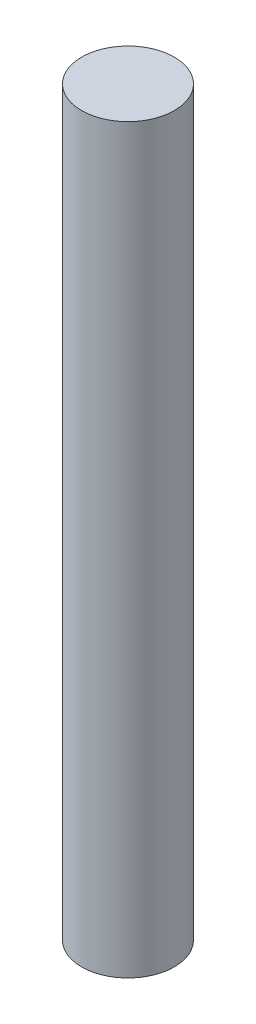
SolidWorks part; units mm, degrees
ref_plane "Front Plane" through (0, 0, 0) normal (0, 0, 1) x (1, 0, 0)
ref_plane "Top Plane" through (0, 0, 0) normal (0, 1, 0) x (1, 0, 0)
ref_plane "Right Plane" through (0, 0, 0) normal (1, 0, 0) x (0, 0, -1)
sketch "Sketch1" plane through (0, 0, 0) normal (0, 1, 0) x (1, 0, 0)
  circle A0 centre (0, 0) radius 4.7625
  dimension "D1" = 9.525
extrude "Boss-Extrude1" add sketch "Sketch1" along normal mid plane 76.2
cosmetic thread "Cosmetic Thread1" parameters "D2"=7.6327
sketch "Sketch2" plane through (0, -38.1, 0) normal (0, -1, 0) x (1, 0, 0)
  circle A0 centre (0, 0) radius 3.175
  dimension "D1" = 6.35
extrude "Cut-Extrude1" cut sketch "Sketch2" against normal blind 6.35
